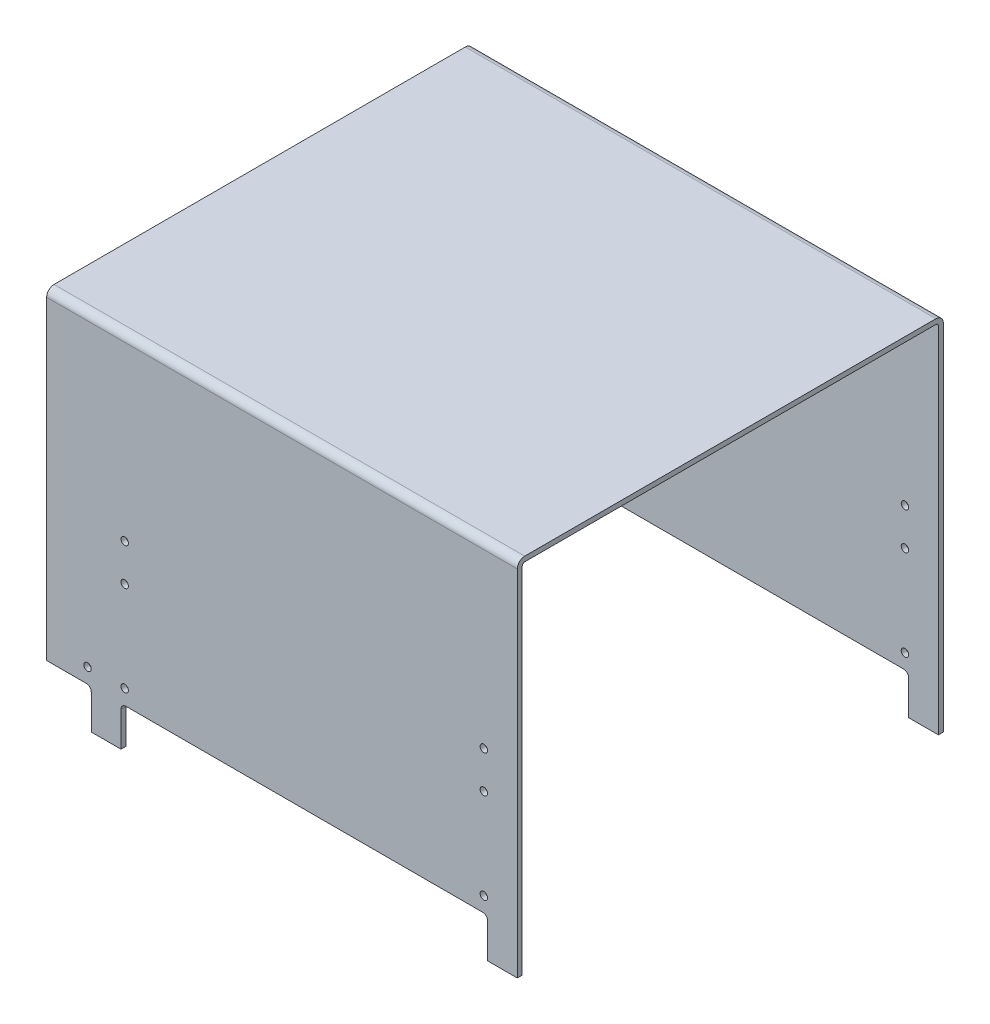
SolidWorks part; units mm, degrees
material "PC High Viscosity"
ref_plane "Front Plane" through (0, 0, 0) normal (0, 0, 1) x (1, 0, 0)
ref_plane "Top Plane" through (0, 0, 0) normal (0, 1, 0) x (1, 0, 0)
ref_plane "Right Plane" through (0, 0, 0) normal (1, 0, 0) x (0, 0, -1)
sketch "Sketch1" plane through (0, 0, 0) normal (1, 0, 0) x (0, 0, -1)
  line L0 (0, 0) -> (0, 463.55)
  line L1 (0, 463.55) -> (546.1, 463.55)
  line L2 (546.1, 463.55) -> (546.1, 0)
  line L3 (6.35, 0) -> (6.35, 457.2)
  line L4 (6.35, 457.2) -> (539.75, 457.2)
  line L5 (539.75, 457.2) -> (539.75, 0)
  line L6 (0, 0) -> (6.35, 0)
  line L7 (546.1, 0) -> (539.75, 0)
  dimension "D1" = 463.55
  dimension "D2" = 546.1
  dimension "D3" = 6.35
extrude "Boss-Extrude1" add sketch "Sketch1" along normal blind 6.35 and the other way blind 596.9
fillet "Fillet1" radius 3.175 2 edges at (-295.275, 457.2, -6.35) (-295.275, 457.2, -539.75)
fillet "Fillet2" radius 9.525 2 edges at (-295.275, 463.55, 0) (-295.275, 463.55, -546.1)
sketch "Sketch2" plane through (0, 0, 0) normal (0, 0, 1) x (1, 0, 0)
  line L0 (-596.9, 0) -> (6.35, 0) construction
  line L1 (-31.75, 0) -> (-501.65, 0)
  line L2 (-31.75, 0) -> (-31.75, 50.8)
  line L3 (-31.75, 50.8) -> (-501.65, 50.8)
  line L4 (-501.65, 0) -> (-501.65, 50.8)
  line L5 (-596.9, 454.025) -> (-596.9, 0) construction
  line L6 (-539.75, 0) -> (-596.9, 0)
  line L7 (-539.75, 0) -> (-539.75, 50.8)
  line L8 (-539.75, 50.8) -> (-596.9, 50.8)
  line L9 (-596.9, 0) -> (-596.9, 50.8)
  line L10 (6.35, 454.025) -> (6.35, 0) construction
  dimension "D1" = 50.8
  dimension "D2" = 469.9
  dimension "D3" = 50.8
  dimension "D5" = 38.1
  dimension "D6" = 38.1
extrude "Cut-Extrude1" cut sketch "Sketch2" against normal through all
fillet "Fillet3" radius 6.35 6 edges at (-539.75, 50.8, -542.925) (-501.65, 50.8, -542.925) (-31.75, 50.8, -542.925) (-31.75, 50.8, -3.175) (-501.65, 50.8, -3.175) (-539.75, 50.8, -3.175)
hole_wizard "3/8 (0.375) Diameter Hole1" positions "Sketch3" profile "Sketch4" hole size "3/8" standard "ANSI Inch" end condition through all
sketch "Sketch3" plane through (0, 0, 0) normal (0, 0, 1) x (1, 0, 0)
  line L0 (6.35, 454.025) -> (6.35, 0) construction
  line L1 (-31.75, 0) -> (6.35, 0) construction
  point P0 (-36.5125, 69.85)
  point P2 (-36.5125, 185.7375)
  point P4 (-36.5125, 233.3625)
  point P6 (-496.8875, 69.85)
  point P8 (-496.8875, 185.7375)
  point P10 (-496.8875, 233.3625)
  point P12 (-544.5125, 69.85)
  dimension "D1" = 42.8625
  dimension "D2" = 503.2375
  dimension "D3" = 550.8625
  dimension "D4" = 69.85
  dimension "D5" = 185.7375
  dimension "D6" = 233.3625
sketch "Sketch4" plane through (-36.5125, 69.85, 0) normal (1, 0, 0) x (0, -1, 0)
  line L0 (0, 0) -> (0, 546.1)
  line L1 (0, 546.1) -> (4.7625, 546.1)
  line L2 (4.7625, 546.1) -> (4.7625, 0)
  line L5 (4.7625, 0) -> (0, 0)
  line L11 (0, -6.35) -> (0, 107.95) construction
  dimension "Thru Hole Dia." = 9.525
  dimension "Thru Hole Depth" = 546.1
